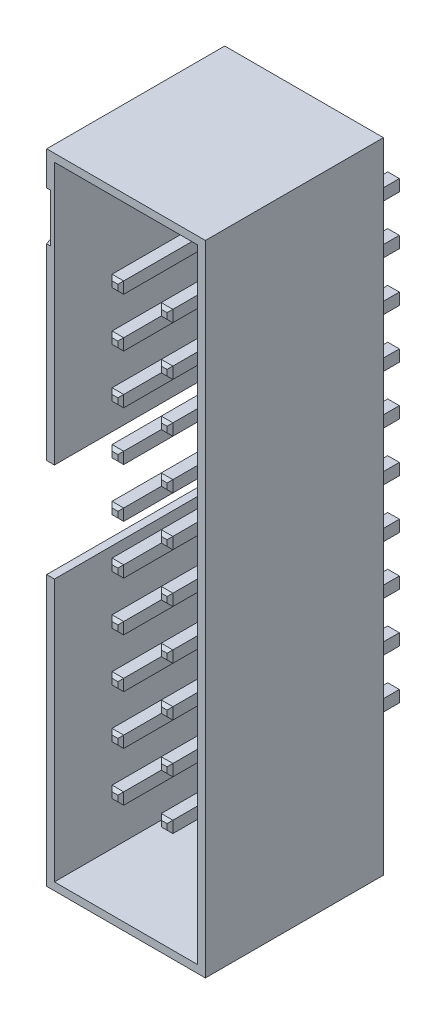
SolidWorks part; units mm, degrees
ref_plane "Plan de face" through (0, 0, 0) normal (0, 0, 1) x (1, 0, 0)
ref_plane "Plan de dessus" through (0, 0, 0) normal (0, 1, 0) x (1, 0, 0)
ref_plane "Plan de droite" through (0, 0, 0) normal (1, 0, 0) x (0, 0, -1)
sketch "Esquisse1" plane through (0, 0, 0) normal (0, 0, 1) x (1, 0, 0)
  line L1 (0, 0) -> (8.2, 0)
  line L2 (0, 0) -> (0, 33)
  line L3 (0, 33) -> (8.2, 33)
  line L4 (8.2, 0) -> (8.2, 33)
  dimension "D1" = 33
  dimension "D2" = 8.2
extrude "Boss.-Extru.1" add sketch "Esquisse1" along normal blind 9.2
sketch "Esquisse2" plane through (0, 0, 9.2) normal (0, 0, 1) x (1, 0, 0)
  line L0 (4.1, 16.5) -> (4.1, 33) construction
  line L1 (0.4, 0.4) -> (7.8, 0.4)
  line L2 (0.4, 0.4) -> (0.4, 32.6)
  line L3 (0.4, 32.6) -> (7.8, 32.6)
  line L4 (7.8, 0.4) -> (7.8, 32.6)
  line L5 (0.4, 0.4) -> (7.8, 32.6) construction
  line L6 (0.4, 32.6) -> (7.8, 0.4) construction
  line L7 (8.2, 33) -> (0, 33) construction
  line L8 (4.1, 16.5) -> (8.2, 16.5) construction
  line L9 (8.2, 0) -> (8.2, 33) construction
  line L10 (0, 33) -> (0, 0) construction
  point P0 (4.1, 16.5)
  dimension "D1" = 0.4
  dimension "D2" = 0.4
extrude "Enlèv. mat.-Extru.1" cut sketch "Esquisse2" against normal blind 8
sketch "Esquisse3" plane through (0, 0, 0) normal (0, 0, -1) x (-1, 0, 0)
  line L0 (-5.37, 27.93) -> (-8.2, 27.93) construction
  line L1 (-5.67, 28.23) -> (-5.07, 28.23)
  line L2 (-5.67, 28.23) -> (-5.67, 27.63)
  line L3 (-5.67, 27.63) -> (-5.07, 27.63)
  line L4 (-5.07, 28.23) -> (-5.07, 27.63)
  line L5 (-5.67, 28.23) -> (-5.07, 27.63) construction
  line L6 (-5.67, 27.63) -> (-5.07, 28.23) construction
  line L7 (-3.13, 28.23) -> (-2.53, 28.23)
  line L8 (-3.13, 28.23) -> (-3.13, 27.63)
  line L9 (-3.13, 27.63) -> (-2.53, 27.63)
  line L10 (-2.53, 28.23) -> (-2.53, 27.63)
  line L11 (-3.13, 28.23) -> (-2.53, 27.63) construction
  line L12 (-3.13, 27.63) -> (-2.53, 28.23) construction
  line L13 (-8.2, 0) -> (-8.2, 33) construction
  line L14 (-2.83, 27.93) -> (0, 27.93) construction
  line L15 (0, 33) -> (0, 0) construction
  line L16 (-5.37, 27.93) -> (-2.83, 27.93) construction
  line L41 (-5.67, 25.69) -> (-5.07, 25.69)
  line L42 (-5.67, 25.69) -> (-5.67, 25.09)
  line L43 (-5.67, 25.09) -> (-5.07, 25.09)
  line L44 (-5.07, 25.69) -> (-5.07, 25.09)
  line L45 (-3.13, 25.69) -> (-2.53, 25.69)
  line L46 (-3.13, 25.69) -> (-3.13, 25.09)
  line L55 (-3.13, 25.09) -> (-2.53, 25.09)
  line L72 (-2.53, 25.69) -> (-2.53, 25.09)
  line L73 (-5.37, 25.39) -> (-8.2, 25.39) construction
  line L74 (-5.67, 25.69) -> (-5.07, 25.09) construction
  line L75 (-5.67, 25.09) -> (-5.07, 25.69) construction
  line L76 (-3.13, 25.69) -> (-2.53, 25.09) construction
  line L77 (-3.13, 25.09) -> (-2.53, 25.69) construction
  line L78 (-2.83, 25.39) -> (0, 25.39) construction
  line L80 (-5.37, 25.39) -> (-2.83, 25.39) construction
  line L81 (-5.67, 23.15) -> (-5.07, 23.15)
  line L82 (-5.67, 23.15) -> (-5.67, 22.55)
  line L91 (-5.67, 22.55) -> (-5.07, 22.55)
  line L92 (-5.07, 23.15) -> (-5.07, 22.55)
  line L93 (-3.13, 23.15) -> (-2.53, 23.15)
  line L94 (-3.13, 23.15) -> (-3.13, 22.55)
  line L95 (-3.13, 22.55) -> (-2.53, 22.55)
  line L96 (-2.53, 23.15) -> (-2.53, 22.55)
  line L97 (-5.37, 22.85) -> (-8.2, 22.85) construction
  line L106 (-5.67, 23.15) -> (-5.07, 22.55) construction
  line L107 (-5.67, 22.55) -> (-5.07, 23.15) construction
  line L108 (-3.13, 23.15) -> (-2.53, 22.55) construction
  line L109 (-3.13, 22.55) -> (-2.53, 23.15) construction
  line L110 (-2.83, 22.85) -> (0, 22.85) construction
  line L111 (-5.37, 22.85) -> (-2.83, 22.85) construction
  line L112 (-5.67, 20.61) -> (-5.07, 20.61)
  line L121 (-5.67, 20.61) -> (-5.67, 20.01)
  line L122 (-5.67, 20.01) -> (-5.07, 20.01)
  line L123 (-5.07, 20.61) -> (-5.07, 20.01)
  line L124 (-3.13, 20.61) -> (-2.53, 20.61)
  line L125 (-3.13, 20.61) -> (-3.13, 20.01)
  line L126 (-3.13, 20.01) -> (-2.53, 20.01)
  line L127 (-2.53, 20.61) -> (-2.53, 20.01)
  line L136 (-5.37, 20.31) -> (-8.2, 20.31) construction
  line L137 (-5.67, 20.61) -> (-5.07, 20.01) construction
  line L138 (-5.67, 20.01) -> (-5.07, 20.61) construction
  line L139 (-3.13, 20.61) -> (-2.53, 20.01) construction
  line L140 (-3.13, 20.01) -> (-2.53, 20.61) construction
  line L141 (-2.83, 20.31) -> (0, 20.31) construction
  line L142 (-5.37, 20.31) -> (-2.83, 20.31) construction
  line L151 (-5.67, 18.07) -> (-5.07, 18.07)
  line L152 (-5.67, 18.07) -> (-5.67, 17.47)
  line L153 (-5.67, 17.47) -> (-5.07, 17.47)
  line L154 (-5.07, 18.07) -> (-5.07, 17.47)
  line L155 (-3.13, 18.07) -> (-2.53, 18.07)
  line L156 (-3.13, 18.07) -> (-3.13, 17.47)
  line L157 (-3.13, 17.47) -> (-2.53, 17.47)
  line L158 (-2.53, 18.07) -> (-2.53, 17.47)
  line L160 (-5.37, 17.77) -> (-8.2, 17.77) construction
  line L161 (-5.67, 18.07) -> (-5.07, 17.47) construction
  line L162 (-5.67, 17.47) -> (-5.07, 18.07) construction
  line L163 (-3.13, 18.07) -> (-2.53, 17.47) construction
  line L164 (-3.13, 17.47) -> (-2.53, 18.07) construction
  line L165 (-2.83, 17.77) -> (0, 17.77) construction
  line L166 (-5.37, 17.77) -> (-2.83, 17.77) construction
  line L167 (-5.67, 15.53) -> (-5.07, 15.53)
  line L168 (-5.67, 15.53) -> (-5.67, 14.93)
  line L169 (-5.67, 14.93) -> (-5.07, 14.93)
  line L170 (-5.07, 15.53) -> (-5.07, 14.93)
  line L171 (-3.13, 15.53) -> (-2.53, 15.53)
  line L172 (-3.13, 15.53) -> (-3.13, 14.93)
  line L173 (-3.13, 14.93) -> (-2.53, 14.93)
  line L174 (-2.53, 15.53) -> (-2.53, 14.93)
  line L175 (-5.37, 15.23) -> (-8.2, 15.23) construction
  line L176 (-5.67, 15.53) -> (-5.07, 14.93) construction
  line L177 (-5.67, 14.93) -> (-5.07, 15.53) construction
  line L178 (-3.13, 15.53) -> (-2.53, 14.93) construction
  line L179 (-3.13, 14.93) -> (-2.53, 15.53) construction
  line L180 (-2.83, 15.23) -> (0, 15.23) construction
  line L181 (-5.37, 15.23) -> (-2.83, 15.23) construction
  line L182 (-5.67, 12.99) -> (-5.07, 12.99)
  line L183 (-5.67, 12.99) -> (-5.67, 12.39)
  line L184 (-5.67, 12.39) -> (-5.07, 12.39)
  line L185 (-5.07, 12.99) -> (-5.07, 12.39)
  line L186 (-3.13, 12.99) -> (-2.53, 12.99)
  line L187 (-3.13, 12.99) -> (-3.13, 12.39)
  line L188 (-3.13, 12.39) -> (-2.53, 12.39)
  line L189 (-2.53, 12.99) -> (-2.53, 12.39)
  line L190 (-5.37, 12.69) -> (-8.2, 12.69) construction
  line L191 (-5.67, 12.99) -> (-5.07, 12.39) construction
  line L192 (-5.67, 12.39) -> (-5.07, 12.99) construction
  line L193 (-3.13, 12.99) -> (-2.53, 12.39) construction
  line L194 (-3.13, 12.39) -> (-2.53, 12.99) construction
  line L195 (-2.83, 12.69) -> (0, 12.69) construction
  line L196 (-5.37, 12.69) -> (-2.83, 12.69) construction
  line L197 (-5.67, 10.45) -> (-5.07, 10.45)
  line L198 (-5.67, 10.45) -> (-5.67, 9.85)
  line L199 (-5.67, 9.85) -> (-5.07, 9.85)
  line L200 (-5.07, 10.45) -> (-5.07, 9.85)
  line L201 (-3.13, 10.45) -> (-2.53, 10.45)
  line L202 (-3.13, 10.45) -> (-3.13, 9.85)
  line L203 (-3.13, 9.85) -> (-2.53, 9.85)
  line L204 (-2.53, 10.45) -> (-2.53, 9.85)
  line L205 (-5.37, 10.15) -> (-8.2, 10.15) construction
  line L206 (-5.67, 10.45) -> (-5.07, 9.85) construction
  line L207 (-5.67, 9.85) -> (-5.07, 10.45) construction
  line L208 (-3.13, 10.45) -> (-2.53, 9.85) construction
  line L209 (-3.13, 9.85) -> (-2.53, 10.45) construction
  line L210 (-2.83, 10.15) -> (0, 10.15) construction
  line L211 (-5.37, 10.15) -> (-2.83, 10.15) construction
  line L212 (-5.67, 7.91) -> (-5.07, 7.91)
  line L213 (-5.67, 7.91) -> (-5.67, 7.31)
  line L214 (-5.67, 7.31) -> (-5.07, 7.31)
  line L215 (-5.07, 7.91) -> (-5.07, 7.31)
  line L216 (-3.13, 7.91) -> (-2.53, 7.91)
  line L217 (-3.13, 7.91) -> (-3.13, 7.31)
  line L218 (-3.13, 7.31) -> (-2.53, 7.31)
  line L219 (-2.53, 7.91) -> (-2.53, 7.31)
  line L220 (-5.37, 7.61) -> (-8.2, 7.61) construction
  line L221 (-5.67, 7.91) -> (-5.07, 7.31) construction
  line L222 (-5.67, 7.31) -> (-5.07, 7.91) construction
  line L223 (-3.13, 7.91) -> (-2.53, 7.31) construction
  line L224 (-3.13, 7.31) -> (-2.53, 7.91) construction
  line L225 (-2.83, 7.61) -> (0, 7.61) construction
  line L226 (-5.37, 7.61) -> (-2.83, 7.61) construction
  line L227 (-5.67, 5.37) -> (-5.07, 5.37)
  line L228 (-5.67, 5.37) -> (-5.67, 4.77)
  line L229 (-5.67, 4.77) -> (-5.07, 4.77)
  line L230 (-5.07, 5.37) -> (-5.07, 4.77)
  line L231 (-3.13, 5.37) -> (-2.53, 5.37)
  line L232 (-3.13, 5.37) -> (-3.13, 4.77)
  line L233 (-3.13, 4.77) -> (-2.53, 4.77)
  line L234 (-2.53, 5.37) -> (-2.53, 4.77)
  line L235 (-5.37, 5.07) -> (-8.2, 5.07) construction
  line L236 (-5.67, 5.37) -> (-5.07, 4.77) construction
  line L237 (-5.67, 4.77) -> (-5.07, 5.37) construction
  line L238 (-3.13, 5.37) -> (-2.53, 4.77) construction
  line L239 (-3.13, 4.77) -> (-2.53, 5.37) construction
  line L240 (-2.83, 5.07) -> (0, 5.07) construction
  line L241 (-5.37, 5.07) -> (-2.83, 5.07) construction
  line L242 (-5.37, 5.07) -> (-5.37, 0) construction
  line L243 (0, 0) -> (-8.2, 0) construction
  line L244 (-5.37, 27.93) -> (-5.37, 33) construction
  line L245 (-8.2, 33) -> (0, 33) construction
  point P0 (-5.37, 27.93)
  point P5 (-2.83, 27.93)
  point P19 (-5.37, 25.39)
  point P24 (-2.83, 25.39)
  point P33 (-5.37, 22.85)
  point P38 (-2.83, 22.85)
  point P47 (-5.37, 20.31)
  point P52 (-2.83, 20.31)
  point P61 (-5.37, 17.77)
  point P66 (-2.83, 17.77)
  point P75 (-5.37, 15.23)
  point P80 (-2.83, 15.23)
  point P89 (-5.37, 12.69)
  point P94 (-2.83, 12.69)
  point P103 (-5.37, 10.15)
  point P108 (-2.83, 10.15)
  point P117 (-5.37, 7.61)
  point P122 (-2.83, 7.61)
  point P131 (-5.37, 5.07)
  point P136 (-2.83, 5.07)
  dimension "D1" = 2.54
  dimension "D2" = 0.6
  dimension "D4" = 2.54
  dimension "D3" = 10
extrude "Boss.-Extru.2" add sketch "Esquisse3" along normal blind 3.5 and the other way blind 8.5
chamfer "Chanfrein1" distance 0.15 angle 45 160 edges at (5.37, 28.23, 8.5) (5.67, 27.93, 8.5) (5.37, 27.63, 8.5) (5.07, 27.93, 8.5) (2.83, 28.23, 8.5) (3.13, 27.93, 8.5) (2.83, 27.63, 8.5) (2.53, 27.93, 8.5) (2.83, 27.63, -3.5) (3.13, 27.93, -3.5) (2.83, 28.23, -3.5) (2.53, 27.93, -3.5) (5.37, 27.63, -3.5) (5.67, 27.93, -3.5) (5.37, 28.23, -3.5) (5.07, 27.93, -3.5) (2.83, 25.09, -3.5) (3.13, 25.39, -3.5) (2.83, 25.69, -3.5) (2.53, 25.39, -3.5) (5.37, 25.09, -3.5) (5.67, 25.39, -3.5) (5.37, 25.69, -3.5) (5.07, 25.39, -3.5) (5.37, 22.55, -3.5) (5.67, 22.85, -3.5) (5.37, 23.15, -3.5) (5.07, 22.85, -3.5) (2.83, 22.55, -3.5) (3.13, 22.85, -3.5) (2.83, 23.15, -3.5) (2.53, 22.85, -3.5) (2.83, 20.01, -3.5) (3.13, 20.31, -3.5) (2.83, 20.61, -3.5) (2.53, 20.31, -3.5) (5.37, 20.01, -3.5) (5.67, 20.31, -3.5) (5.37, 20.61, -3.5) (5.07, 20.31, -3.5) (5.37, 17.47, -3.5) (5.67, 17.77, -3.5) (5.37, 18.07, -3.5) (5.07, 17.77, -3.5) (2.83, 17.47, -3.5) (3.13, 17.77, -3.5) (2.83, 18.07, -3.5) (2.53, 17.77, -3.5) (2.83, 14.93, -3.5) (3.13, 15.23, -3.5) (2.83, 15.53, -3.5) (2.53, 15.23, -3.5) (5.37, 14.93, -3.5) (5.67, 15.23, -3.5) (5.37, 15.53, -3.5) (5.07, 15.23, -3.5) (5.37, 25.69, 8.5) (5.67, 25.39, 8.5) (5.37, 25.09, 8.5) (5.07, 25.39, 8.5) (5.37, 23.15, 8.5) (5.67, 22.85, 8.5) (5.37, 22.55, 8.5) (5.07, 22.85, 8.5) (5.37, 20.61, 8.5) (5.67, 20.31, 8.5) (5.37, 20.01, 8.5) (5.07, 20.31, 8.5) (5.37, 18.07, 8.5) (5.67, 17.77, 8.5) (5.37, 17.47, 8.5) (5.07, 17.77, 8.5) (5.37, 15.53, 8.5) (5.67, 15.23, 8.5) (5.37, 14.93, 8.5) (5.07, 15.23, 8.5) (5.37, 12.99, 8.5) (5.67, 12.69, 8.5) (5.37, 12.39, 8.5) (5.07, 12.69, 8.5) (5.37, 10.45, 8.5) (5.67, 10.15, 8.5) (5.37, 9.85, 8.5) (5.07, 10.15, 8.5) (5.37, 7.91, 8.5) (5.67, 7.61, 8.5) (5.37, 7.31, 8.5) (5.07, 7.61, 8.5) (5.37, 5.37, 8.5) (5.67, 5.07, 8.5) (5.37, 4.77, 8.5) (5.07, 5.07, 8.5) (2.83, 5.37, 8.5) (3.13, 5.07, 8.5) (2.83, 4.77, 8.5) (2.53, 5.07, 8.5) (2.83, 7.91, 8.5) (3.13, 7.61, 8.5) (2.83, 7.31, 8.5) (2.53, 7.61, 8.5) (2.83, 10.45, 8.5) (3.13, 10.15, 8.5) (2.83, 9.85, 8.5) (2.53, 10.15, 8.5) (2.83, 12.99, 8.5) (3.13, 12.69, 8.5) (2.83, 12.39, 8.5) (2.53, 12.69, 8.5) (2.83, 15.53, 8.5) (3.13, 15.23, 8.5) (2.83, 14.93, 8.5) (2.53, 15.23, 8.5) (2.83, 18.07, 8.5) (3.13, 17.77, 8.5) (2.83, 17.47, 8.5) (2.53, 17.77, 8.5) (2.83, 20.61, 8.5) (3.13, 20.31, 8.5) (2.83, 20.01, 8.5) (2.53, 20.31, 8.5) (2.83, 23.15, 8.5) (3.13, 22.85, 8.5) (2.83, 22.55, 8.5) (2.53, 22.85, 8.5) (2.83, 25.69, 8.5) (3.13, 25.39, 8.5) (2.83, 25.09, 8.5) (2.53, 25.39, 8.5) (2.83, 9.85, -3.5) (3.13, 10.15, -3.5) (2.83, 10.45, -3.5) (2.53, 10.15, -3.5) (2.83, 12.39, -3.5) (3.13, 12.69, -3.5) (2.83, 12.99, -3.5) (2.53, 12.69, -3.5) (5.37, 12.39, -3.5) (5.67, 12.69, -3.5) (5.37, 12.99, -3.5) (5.07, 12.69, -3.5) (5.37, 9.85, -3.5) (5.67, 10.15, -3.5) (5.37, 10.45, -3.5) (5.07, 10.15, -3.5) (5.37, 7.31, -3.5) (5.67, 7.61, -3.5) (5.37, 7.91, -3.5) (5.07, 7.61, -3.5) (2.83, 7.31, -3.5) (3.13, 7.61, -3.5) (2.83, 7.91, -3.5) (2.53, 7.61, -3.5) (2.83, 4.77, -3.5) (3.13, 5.07, -3.5) (2.83, 5.37, -3.5) (2.53, 5.07, -3.5) (5.37, 4.77, -3.5) (5.67, 5.07, -3.5) (5.37, 5.37, -3.5) (5.07, 5.07, -3.5)
sketch "Esquisse4" plane through (0, 0, 9.2) normal (0, 0, 1) x (1, 0, 0)
  line L0 (0, 33) -> (0, 0) construction
  line L1 (0, 19.05) -> (0.4, 19.05)
  line L2 (0, 19.05) -> (0, 13.95)
  line L3 (0, 13.95) -> (0.4, 13.95)
  line L4 (0.4, 19.05) -> (0.4, 13.95)
  line L5 (0.4, 32.6) -> (0.4, 0.4) construction
  line L6 (0, 0) -> (0, 13.95) construction
  line L7 (0, 33) -> (0, 19.05) construction
  dimension "D1" = 5.1
extrude "Enlèv. mat.-Extru.2" cut sketch "Esquisse4" against normal up to surface (8 mm away) up to face at (2.83, 5.07, 1.2)
sketch "Esquisse5" plane through (0, 0, 0) normal (-1, 0, 0) x (0, 0, 1)
  line L0 (9.2, 31.25) -> (9.2, 28.75)
  line L1 (9.2, 33) -> (9.2, 19.05) construction
  line L2 (9.2, 28.75) -> (7.0349, 30)
  line L3 (7.0349, 30) -> (9.2, 31.25)
  line L4 (9.2, 33) -> (0, 33) construction
  dimension "D1" = 2.5
  dimension "D2" = 3
extrude "Enlèv. mat.-Extru.3" cut sketch "Esquisse5" against normal blind 0.2
